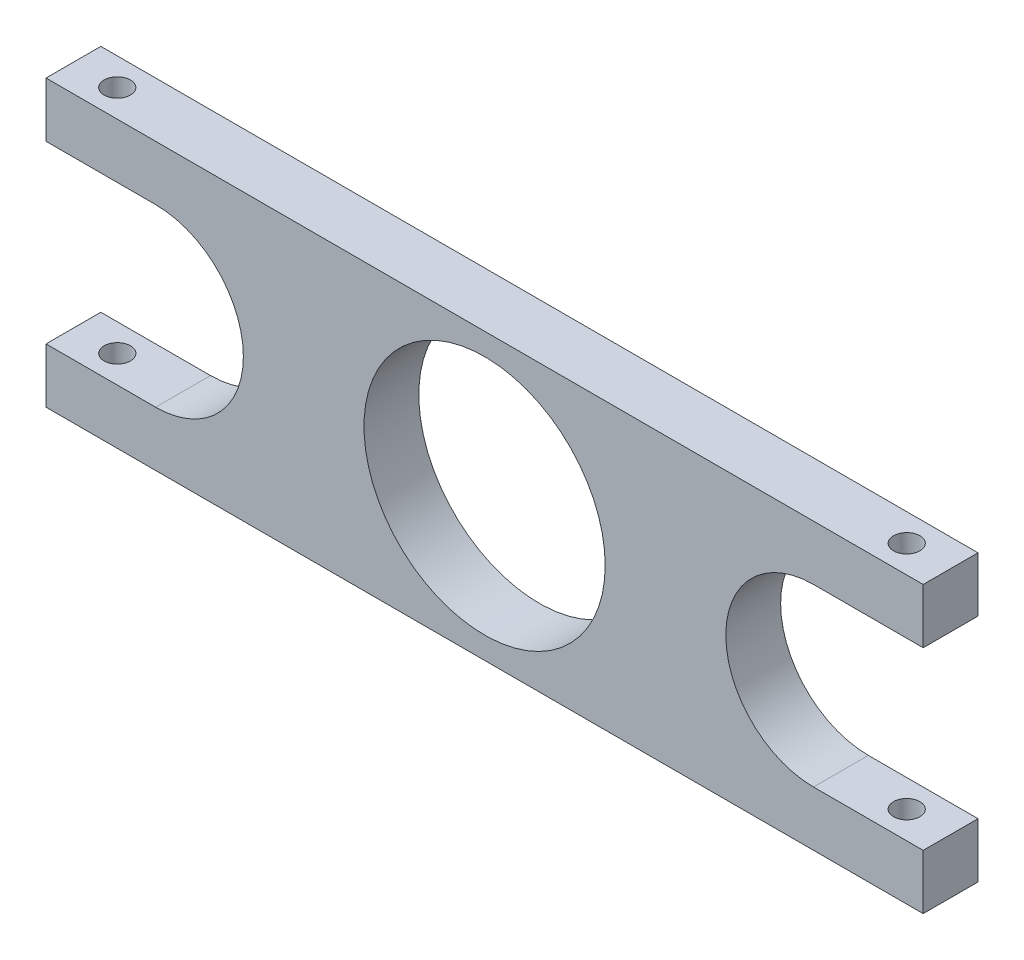
SolidWorks part; units mm, degrees
material "ABS"
ref_plane "Plan de face" through (0, 0, 0) normal (0, 0, 1) x (1, 0, 0)
ref_plane "Plan de dessus" through (0, 0, 0) normal (0, 1, 0) x (1, 0, 0)
ref_plane "Plan de droite" through (0, 0, 0) normal (1, 0, 0) x (0, 0, -1)
sketch "Esquisse1" plane through (0, 0, 0) normal (0, 0, 1) x (1, 0, 0)
  line L0 (0, 0) -> (80, 0)
  line L1 (80, 0) -> (80, 5)
  line L2 (80, 5) -> (70, 5)
  line L4 (70, 21) -> (80, 21)
  line L5 (80, 21) -> (80, 26)
  line L6 (80, 26) -> (0, 26)
  line L7 (0, 26) -> (0, 21)
  line L8 (0, 21) -> (10, 21)
  line L10 (10, 5) -> (0, 5)
  line L11 (0, 5) -> (0, 0)
  arc A0 (10, 21) -> (10, 5) centre (10, 13) cw
  arc A1 (70, 21) -> (70, 5) centre (70, 13) ccw
  circle A2 centre (40, 13) radius 11
  dimension "D10" = 22
  dimension "D1" = 80
  dimension "D2" = 80
  dimension "D3" = 10
  dimension "D4" = 10
  dimension "D5" = 26
  dimension "D6" = 5
  dimension "D7" = 5
  dimension "D8" = 5
  dimension "D9" = 5
  dimension "D11" = 13
  dimension "D12" = 40
extrude "Boss.-Extru.1" add sketch "Esquisse1" along normal blind 5
hole_wizard "Dégagement M21" positions "Esquisse2" profile "Esquisse3" size "M2" standard "ISO" slot yes end condition through all
sketch "Esquisse2" plane through (0, 26, 0) normal (0, 1, 0) x (1, 0, 0)
  line L0 (0, -5) -> (0, 0) construction
  line L1 (80, -5) -> (80, 0) construction
  line L3 (80, 0) -> (0, 0) construction
  point P0 (76, -2.5)
  point P2 (4, -2.5)
  dimension "D1" = 4
  dimension "D2" = 4
  dimension "D3" = 2.5
  dimension "D4" = 2.5
sketch "Esquisse3" plane through (76, 26, 2.5) normal (1, 0, 0) x (0, 0, 1)
  line L0 (0, 0) -> (0, 26)
  line L1 (0, 26) -> (1.2, 26)
  line L2 (1.2, 26) -> (1.2, 0)
  line L5 (1.2, 0) -> (0, 0)
  line L11 (0, -6.35) -> (0, 107.95) construction
  dimension "Diamètre du perçage jusqu'au prochain" = 2.4
  dimension "Profondeur du perçage jusqu'au prochain" = 26
equation "\"D3@Esquisse2\"=\"D1@Boss.-Extru.1\"/2"
equation "\"D4@Esquisse2\"=\"D1@Boss.-Extru.1\"/2"
